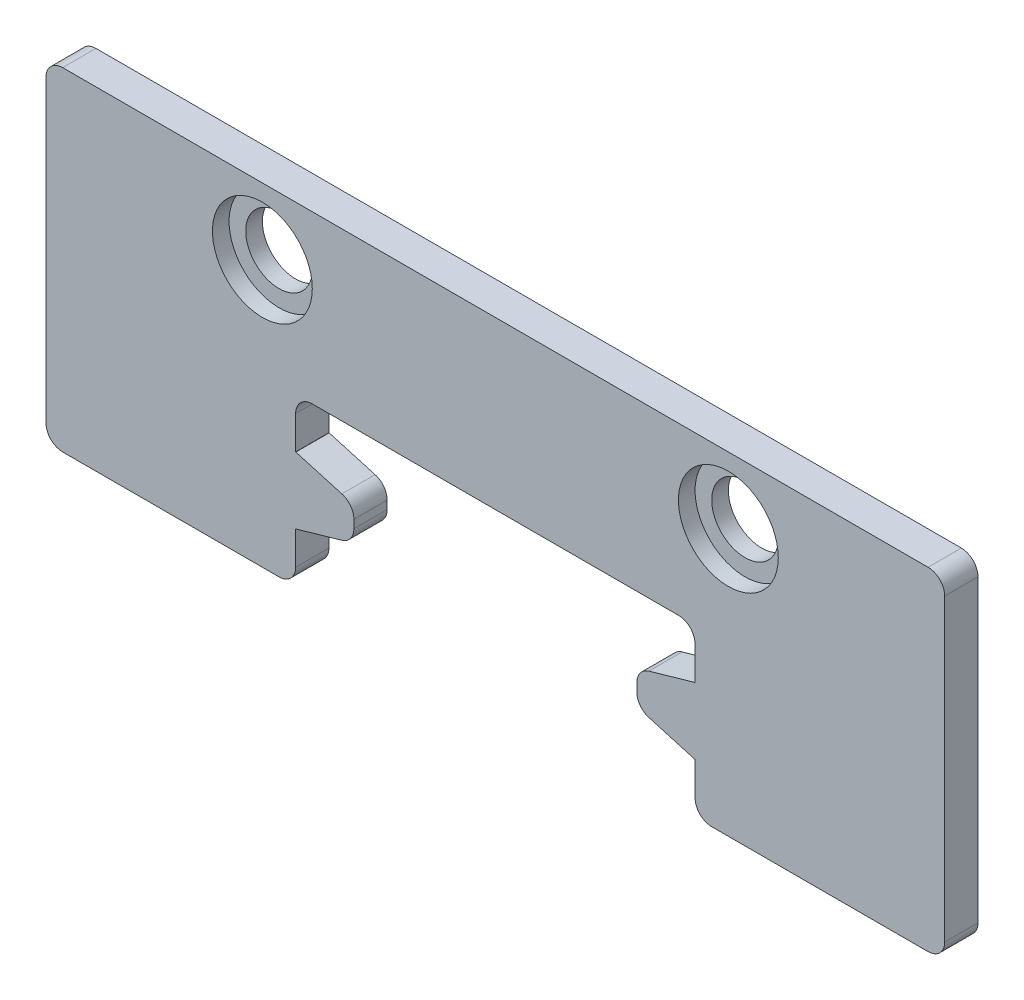
SolidWorks part; units mm, degrees
ref_plane "Front Plane" through (0, 0, 0) normal (0, 0, 1) x (1, 0, 0)
ref_plane "Top Plane" through (0, 0, 0) normal (0, 1, 0) x (1, 0, 0)
ref_plane "Right Plane" through (0, 0, 0) normal (1, 0, 0) x (0, 0, -1)
sketch "Sketch1" plane through (0, 0, 0) normal (0, 0, 1) x (1, 0, 0)
  line L0 (-6, -1.5) -> (-6, 0)
  line L1 (-13.5, 5) -> (13.5, 5)
  line L2 (-13.5, 5) -> (-13.5, -5)
  line L3 (-13.5, -5) -> (-6, -5)
  line L4 (13.5, 5) -> (13.5, -5)
  line L5 (-13.5, 5) -> (13.5, -5) construction
  line L6 (-13.5, -5) -> (13.5, 5) construction
  line L8 (-6, -5) -> (-6, -3.5)
  line L9 (-6, 0) -> (6, 0)
  line L10 (6, -5) -> (6, -3.5)
  line L11 (-6, -1.5) -> (-4.25, -1.5)
  line L13 (-6, -3.5) -> (-4.25, -3.5)
  line L14 (-4.25, -1.5) -> (-4.25, -3.5)
  line L15 (6, -1.5) -> (4.25, -1.5)
  line L17 (6, -3.5) -> (4.25, -3.5)
  line L18 (4.25, -1.5) -> (4.25, -3.5)
  line L19 (6, -1.5) -> (6, 0)
  line L20 (6, -5) -> (13.5, -5)
  point P0 (0, 0)
  dimension "D1" = 27
  dimension "D2" = 10
  dimension "D3" = 12
  dimension "D4" = 6
  dimension "D5" = 5
  dimension "D6" = 8.5
  dimension "D7" = 4.25
  dimension "D8" = 2
  dimension "D9" = 2
  dimension "D10" = 1.5
  dimension "D11" = 1.5
extrude "Boss-Extrude1" add sketch "Sketch1" along normal blind 1
chamfer "Chamfer1" distance 0.5 angle 74 4 edges at (4.25, -3.5, 0.5) (4.25, -1.5, 0.5) (-4.25, -3.5, 0.5) (-4.25, -1.5, 0.5)
fillet "Fillet1" radius 0.5 4 edges at (-4.25, -3, 0.5) (-4.25, -2, 0.5) (4.25, -3, 0.5) (4.25, -2, 0.5)
sketch "Sketch2" plane through (0, 0, 1) normal (0, 0, 1) x (1, 0, 0)
  line L0 (13.5, 5) -> (-13.5, 5) construction
  circle A0 centre (-7, 3) radius 1
  circle A1 centre (7, 3) radius 1
  dimension "D3" = 2
  dimension "D4" = 2
  dimension "D1" = 14
  dimension "D2" = 7
  dimension "D5" = 2
  dimension "D6" = 2
extrude "Cut-Extrude1" cut sketch "Sketch2" against normal blind 1
fillet "Fillet2" radius 0.5 8 edges at (13.5, 5, 0.5) (13.5, -5, 0.5) (6, -5, 0.5) (6, 0, 0.5) (-6, 0, 0.5) (-6, -5, 0.5) (-13.5, -5, 0.5) (-13.5, 5, 0.5)
sketch "Sketch3" plane through (0, 0, 1) normal (0, 0, 1) x (1, 0, 0)
  circle A0 centre (-7, 3) radius 1.5
  circle A1 centre (7, 3) radius 1.5
  dimension "D1" = 3
  dimension "D2" = 3
extrude "Cut-Extrude2" cut sketch "Sketch3" against normal blind 0.5
